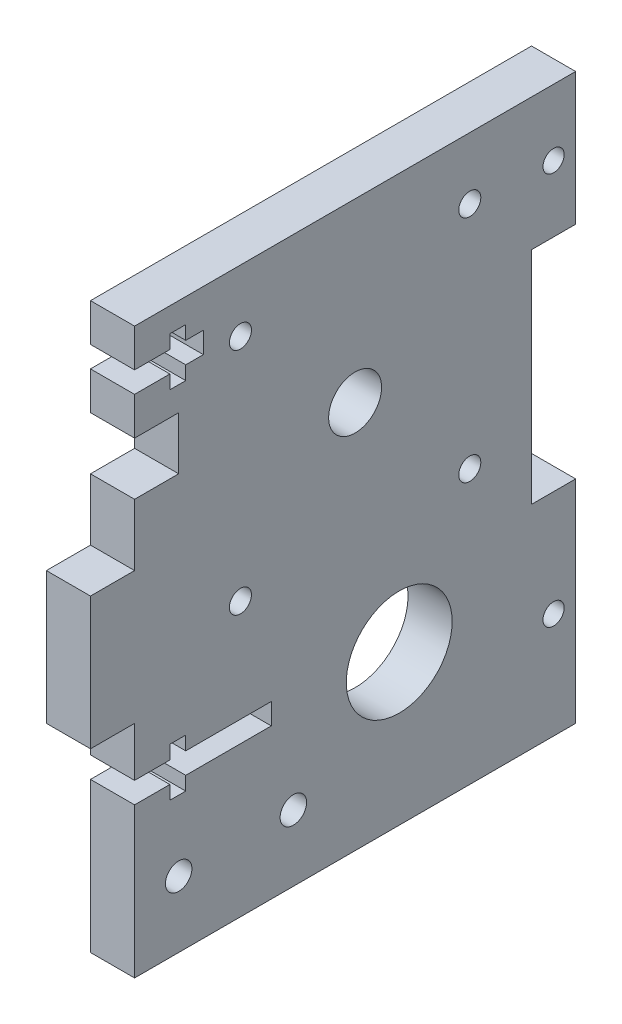
SolidWorks part; units mm, degrees
material "Acrylic (Medium-high impact)"
ref_plane "Front Plane" through (0, 0, 0) normal (0, 0, 1) x (1, 0, 0)
ref_plane "Top Plane" through (0, 0, 0) normal (0, 1, 0) x (1, 0, 0)
ref_plane "Right Plane" through (0, 0, 0) normal (1, 0, 0) x (0, 0, -1)
sketch "Sketch1" plane through (0, 0, 0) normal (1, 0, 0) x (0, 0, -1)
  line L0 (0, 0) -> (-50, 0)
  line L1 (-50, 53) -> (-50, 64)
  line L2 (-50, 25) -> (-50, 0)
  line L3 (-45, 50) -> (-55.472, 50) construction
  line L4 (-25, 64) -> (-25, 0) construction
  line L5 (-38.5, 19.4) -> (-38.5, 17) construction
  line L6 (-50, 25) -> (-55, 25)
  line L7 (-55, 25) -> (-55, 40)
  line L8 (-55, 40) -> (-50, 40)
  line L9 (-50, 40) -> (-50, 47)
  line L10 (-50, 47) -> (-45, 47)
  line L11 (-45, 47) -> (-45, 53)
  line L12 (-45, 53) -> (-50, 53)
  line L13 (-42.5, 19.4) -> (-34.5, 19.4)
  line L14 (-42.5, 19.4) -> (-42.5, 17)
  line L15 (-42.5, 17) -> (-34.5, 17)
  line L16 (-34.5, 19.4) -> (-34.5, 17)
  line L17 (-34.5, 18.2) -> (-42.5, 18.2) construction
  line L18 (-50, 64) -> (0, 64)
  line L19 (0, 64) -> (0, 49)
  line L20 (0, 49) -> (-5, 49)
  line L21 (-5, 49) -> (-5, 24)
  line L22 (-5, 24) -> (0, 24)
  line L23 (0, 24) -> (0, 0)
  line L24 (-20, 64) -> (-20, 0) construction
  circle A0 centre (-20, 17) radius 6
  circle A1 centre (-25, 44) radius 3
  circle A3 centre (-45, 7.5) radius 1.5
  circle A4 centre (-38, 57) radius 1.25
  circle A5 centre (-12, 57) radius 1.25
  circle A6 centre (-38, 31) radius 1.25
  circle A7 centre (-12, 31) radius 1.25
  circle A8 centre (-32, 7.5) radius 1.5
  point P29 (0, 56.5)
  dimension "D9" = 12
  dimension "D10" = 6
  dimension "D15" = 8
  dimension "D16" = 2.4
  dimension "D18" = 6
  dimension "D19" = 2.5
  dimension "D24" = 3
  dimension "D1" = 25
  dimension "D2" = 15
  dimension "D3" = 10
  dimension "D4" = 6
  dimension "D5" = 11
  dimension "D6" = 50
  dimension "D7" = 25
  dimension "D8" = 15
  dimension "D11" = 17
  dimension "D12" = 5
  dimension "D13" = 5
  dimension "D14" = 5
  dimension "D17" = 7.5
  dimension "D20" = 13
  dimension "D21" = 13
  dimension "D25" = 7.5
  dimension "D26" = 6.5
  dimension "D27" = 30
  dimension "D22" = 2
  dimension "D23" = 2
extrude "Boss-Extrude1" add sketch "Sketch1" along normal blind 5
sketch "Sketch2" plane through (0, 0, 0) normal (-1, 0, 0) x (0, 0, 1)
  line L0 (50, 58.5) -> (0, 58.5) construction
  line L1 (50, 64) -> (50, 53) construction
  line L2 (0, 49) -> (0, 64) construction
  line L3 (50, 59.7) -> (46, 59.7)
  line L4 (46, 59.7) -> (46, 61.25)
  line L5 (46, 61.25) -> (44.2, 61.25)
  line L6 (44.2, 61.25) -> (44.2, 59.7)
  line L7 (44.2, 59.7) -> (42.2, 59.7)
  line L8 (42.2, 59.7) -> (42.2, 57.3)
  line L9 (50, 57.3) -> (50, 59.7)
  line L10 (44.2, 57.3) -> (42.2, 57.3)
  line L11 (44.2, 55.75) -> (44.2, 57.3)
  line L12 (46, 55.75) -> (44.2, 55.75)
  line L13 (46, 57.3) -> (46, 55.75)
  line L14 (50, 57.3) -> (46, 57.3)
  line L15 (50, 19.4) -> (46, 19.4)
  line L16 (46, 19.4) -> (46, 20.95)
  line L17 (46, 20.95) -> (44.2, 20.95)
  line L18 (44.2, 20.95) -> (44.2, 19.4)
  line L19 (44.2, 19.4) -> (42.2, 19.4)
  line L20 (42.2, 19.4) -> (42.2, 17)
  line L21 (50, 17) -> (50, 19.4)
  line L22 (44.2, 17) -> (42.2, 17)
  line L23 (44.2, 15.45) -> (44.2, 17)
  line L24 (46, 15.45) -> (44.2, 15.45)
  line L25 (46, 17) -> (46, 15.45)
  line L26 (50, 17) -> (46, 17)
  circle A0 centre (2.5, 56.5) radius 1.2
  circle A1 centre (2.5, 12) radius 1.2
  point P14 (42.2, 58.5)
  point P29 (42.2, 18.2)
  dimension "D7" = 2.4
  dimension "D1" = 4
  dimension "D2" = 1.8
  dimension "D3" = 2
  dimension "D4" = 2.4
  dimension "D5" = 5.5
  dimension "D6" = 2
extrude "Cut-Extrude1" cut sketch "Sketch2" against normal through all
